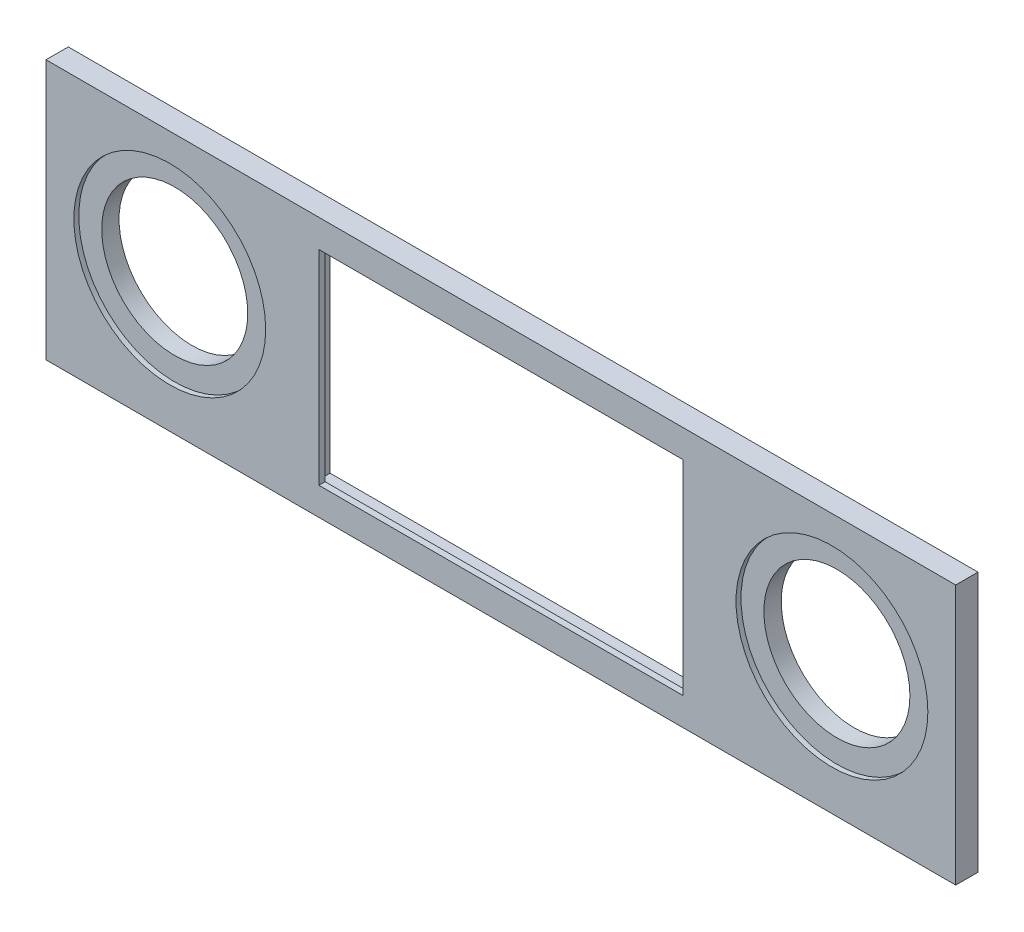
SolidWorks part; units mm, degrees
ref_plane "Front Plane" through (0, 0, 0) normal (0, 0, 1) x (1, 0, 0)
ref_plane "Top Plane" through (0, 0, 0) normal (0, 1, 0) x (1, 0, 0)
ref_plane "Right Plane" through (0, 0, 0) normal (1, 0, 0) x (0, 0, -1)
sketch "Sketch2" plane through (0, 0, 0) normal (0, 0, 1) x (1, 0, 0)
  line L1 (-367.5, -105) -> (367.5, -105)
  line L2 (-367.5, -105) -> (-367.5, 105)
  line L3 (-367.5, 105) -> (367.5, 105)
  line L4 (367.5, -105) -> (367.5, 105)
  line L5 (-367.5, -105) -> (367.5, 105) construction
  line L6 (-367.5, 105) -> (367.5, -105) construction
  line L7 (-147, -82.5) -> (147, -82.5)
  line L8 (-147, -82.5) -> (-147, 82.5)
  line L9 (-147, 82.5) -> (147, 82.5)
  line L10 (147, -82.5) -> (147, 82.5)
  line L11 (-147, -82.5) -> (147, 82.5) construction
  line L12 (-147, 82.5) -> (147, -82.5) construction
  circle A0 centre (-267.5, 5) radius 59
  circle A1 centre (267.5, 5) radius 59
  point P0 (0, 0)
  point P11 (0, 0)
  dimension "D3" = 118
  dimension "D4" = 118
  dimension "D5" = 100
  dimension "D6" = 100
  dimension "D7" = 294
  dimension "D9" = 100
  dimension "D10" = 100
  dimension "D1" = 735
  dimension "D2" = 210
  dimension "D8" = 165
extrude "Boss-Extrude1" add sketch "Sketch2" along normal blind 18
sketch "Sketch3" plane through (0, 0, 18) normal (0, 0, 1) x (1, 0, 0)
  circle A0 centre (-267.5, 5) radius 77.5
  circle A1 centre (267.5, 5) radius 77.5
  dimension "D1" = 155
  dimension "D2" = 155
extrude "Cut-Extrude1" cut sketch "Sketch3" against normal blind 4
sketch "Sketch4" plane through (0, 0, 0) normal (0, 0, -1) x (-1, 0, 0)
  line L1 (-156, -87.5) -> (156, -87.5)
  line L2 (-156, -87.5) -> (-156, 87.5)
  line L3 (-156, 87.5) -> (156, 87.5)
  line L4 (156, -87.5) -> (156, 87.5)
  line L5 (-156, -87.5) -> (156, 87.5) construction
  line L6 (-156, 87.5) -> (156, -87.5) construction
  point P0 (0, 0)
  dimension "D1" = 312
  dimension "D2" = 175
extrude "Cut-Extrude2" cut sketch "Sketch4" against normal blind 13
